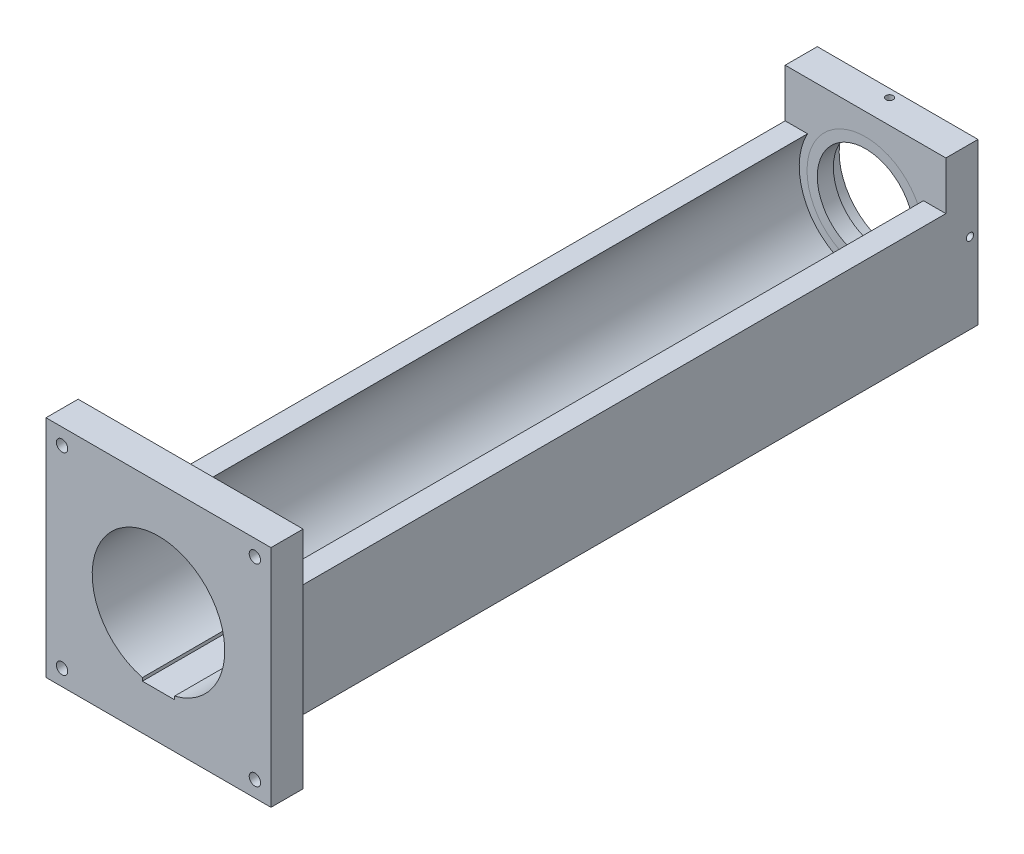
SolidWorks part; units mm, degrees
ref_plane "Front Plane" through (0, 0, 0) normal (0, 0, 1) x (1, 0, 0)
ref_plane "Top Plane" through (0, 0, 0) normal (0, 1, 0) x (1, 0, 0)
ref_plane "Right Plane" through (0, 0, 0) normal (1, 0, 0) x (0, 0, -1)
sketch "Sketch2" plane through (0, 0, 0) normal (0, 0, 1) x (1, 0, 0)
  line L1 (0, 0) -> (63.5, 0)
  line L2 (0, 0) -> (0, 63.5)
  line L3 (0, 63.5) -> (63.5, 63.5)
  line L4 (63.5, 0) -> (63.5, 63.5)
  circle A0 centre (31.75, 31.75) radius 26.1938
  dimension "D3" = 52.3875
  dimension "D4" = 31.75
  dimension "D5" = 31.75
  dimension "D6" = 31.75
  dimension "D7" = 31.75
  dimension "D1" = 63.5
  dimension "D2" = 63.5
extrude "Boss-Extrude1" add sketch "Sketch2" along normal blind 279.4
sketch "Sketch3" plane through (0, 0, 279.4) normal (0, 0, 1) x (1, 0, 0)
  line L0 (63.5, 0) -> (63.5, 63.5) construction
  line L1 (63.5, 63.5) -> (0, 63.5) construction
  line L2 (-12.7, 76.2) -> (76.2, 76.2)
  line L3 (-12.7, 76.2) -> (-12.7, -12.7)
  line L4 (-12.7, -12.7) -> (76.2, -12.7)
  line L5 (76.2, 76.2) -> (76.2, -12.7)
  line L6 (0, 0) -> (63.5, 0) construction
  line L8 (0, -34.925) -> (0, 34.925) construction
  circle A0 centre (31.75, 31.75) radius 26.1938
  circle A4 centre (31.75, 31.75) radius 26.1938 construction
  dimension "D5" = 0
  dimension "D6" = 0
  dimension "D1" = 12.7
  dimension "D2" = 12.7
  dimension "D3" = 12.7
  dimension "D4" = 12.7
extrude "Boss-Extrude2" add sketch "Sketch3" against normal blind 12.7
sketch "Sketch4" plane through (0, 0, 0) normal (0, 0, -1) x (-1, 0, 0)
  line L0 (0, 34.925) -> (0, -34.925) construction
  line L1 (-63.5, 0) -> (0, 0)
  line L2 (-63.5, 0) -> (-63.5, 63.5)
  line L3 (-63.5, 63.5) -> (0, 63.5)
  line L4 (0, 0) -> (0, 63.5)
  line L5 (-63.5, 0) -> (0, 63.5) construction
  line L6 (-63.5, 63.5) -> (0, 0) construction
  line L7 (-63.5, 63.5) -> (0, 63.5) construction
  circle A0 centre (-31.75, 31.75) radius 23.114
  circle A1 centre (-31.75, 31.75) radius 26.1938 construction
  dimension "D1" = 46.228
  dimension "D2" = 0
extrude "Boss-Extrude3" add sketch "Sketch4" along normal blind 12.7
ref_plane "Plane1" through (0, 0, -6.35) normal (0, 0, -1) x (-1, 0, 0)
sketch "Sketch5" plane through (0, 0, -6.35) normal (0, 0, -1) x (-1, 0, 0)
  circle A0 centre (-31.75, 31.75) radius 23.114
  circle A1 centre (-31.75, 31.75) radius 19.05
  circle A2 centre (-31.75, 31.75) radius 23.114 construction
  dimension "D1" = 38.1
  dimension "D2" = 0
extrude "Boss-Extrude4" add sketch "Sketch5" against normal blind 6.35 separate body
sketch "Sketch7" plane through (63.5, 0, 0) normal (1, 0, 0) x (0, 0, -1)
  line L0 (0, 48.895) -> (0, -48.895) construction
  line L1 (-266.7, 63.5) -> (0, 63.5)
  line L2 (-266.7, 63.5) -> (-266.7, 44.45)
  line L3 (-266.7, 44.45) -> (0, 44.45)
  line L4 (0, 63.5) -> (0, 44.45)
  dimension "D1" = 19.05
extrude "Cut-Extrude2" cut sketch "Sketch7" against normal through all
hole_wizard "#6-40 Tapped Hole1" positions "Sketch9" profile "Sketch8" tap size "#6-40" standard "ANSI Inch" end condition through all
sketch "Sketch9" plane through (63.5, 0, 0) normal (1, 0, 0) x (0, 0, -1)
  line L0 (12.7, 63.5) -> (12.7, 0) construction
  line L1 (0, 63.5) -> (12.7, 63.5) construction
  line L2 (48.895, 0) -> (-48.895, 0) construction
  point P0 (9.525, 31.75)
  dimension "D1" = 3.175
  dimension "D2" = 31.75
  dimension "D3" = 31.75
sketch "Sketch8" plane through (63.5, 31.75, -9.525) normal (0, 1, 0) x (0, 0, -1)
  line L0 (0, 0) -> (0, 76.2)
  line L1 (0, 76.2) -> (1.4351, 76.2)
  line L2 (1.4351, 76.2) -> (1.4351, 0)
  line L5 (1.4351, 0) -> (0, 0)
  line L11 (0, -6.35) -> (0, 107.95) construction
  dimension "Thru Tap Drill Dia." = 2.8702
  dimension "Thru Tap Drill Depth" = 76.2
cosmetic thread "Hole Thread1" parameters "D2"=3.5052
hole_wizard "#6-40 Tapped Hole2" positions "Sketch11" profile "Sketch10" tap size "#6-40" standard "ANSI Inch" end condition through all
sketch "Sketch11" plane through (0, 63.5, 0) normal (0, 1, 0) x (1, 0, 0)
  line L0 (63.5, 0) -> (63.5, 12.7) construction
  line L1 (0, 12.7) -> (63.5, 12.7) construction
  point P0 (31.75, 9.525)
  dimension "D1" = 31.75
  dimension "D2" = 3.175
sketch "Sketch10" plane through (31.75, 63.5, -9.525) normal (1, 0, 0) x (0, 0, 1)
  line L0 (0, 0) -> (0, 76.2)
  line L1 (0, 76.2) -> (1.4351, 76.2)
  line L2 (1.4351, 76.2) -> (1.4351, 0)
  line L5 (1.4351, 0) -> (0, 0)
  line L11 (0, -6.35) -> (0, 107.95) construction
  dimension "Thru Tap Drill Dia." = 2.8702
  dimension "Thru Tap Drill Depth" = 76.2
cosmetic thread "Hole Thread2" parameters "D2"=3.5052
hole_wizard "CSK for #8 Flat Head Machine Screw1" positions "Sketch14" profile "Sketch12" countersink size "#8" standard "ANSI Inch" end condition through all
sketch "Sketch14" plane through (0, 0, 266.7) normal (0, 0, -1) x (-1, 0, 0)
  line L0 (-76.2, -12.7) -> (-76.2, 76.2) construction
  line L1 (12.7, 76.2) -> (12.7, -12.7) construction
  line L3 (12.7, -12.7) -> (-76.2, -12.7) construction
  point P0 (-69.85, 69.85)
  point P2 (6.35, 69.85)
  point P4 (6.35, -6.35)
  point P6 (-69.85, -6.35)
  dimension "D1" = 76.2
  dimension "D2" = 6.35
  dimension "D3" = 6.35
  dimension "D4" = 76.2
  dimension "D5" = 6.35
  dimension "D6" = 76.2
  dimension "D7" = 76.2
  dimension "D8" = 6.35
  dimension "D9" = 6.35
sketch "Sketch12" plane through (69.85, 69.85, 266.7) normal (1, 0, 0) x (0, 1, 0)
  line L0 (0, 0) -> (0, 12.7)
  line L1 (0, 12.7) -> (2.2479, 12.7)
  line L2 (2.2479, 12.7) -> (2.2479, 2.2645)
  line L3 (2.2479, 2.2645) -> (4.2164, 0)
  line L5 (4.2164, 0) -> (0, 0)
  line L6 (-2.2479, 2.2645) -> (-4.2164, 0) construction
  line L11 (0, -6.35) -> (0, 107.95) construction
  dimension "Thru Hole Dia." = 4.4958
  dimension "Thru Hole Depth" = 12.7
  dimension "Near C'Sink Dia." = 8.4328
  dimension "Near C'Sink Angle" = 82
sketch "Sketch16" plane through (0, 0, 279.4) normal (0, 0, 1) x (1, 0, 0)
  line L0 (76.2, -12.7) -> (76.2, 76.2) construction
  line L1 (25.4, 5.08) -> (38.1, 5.08)
  line L2 (25.4, 5.08) -> (25.4, 7.6835)
  line L3 (25.4, 7.6835) -> (38.1, 7.6835)
  line L4 (38.1, 5.08) -> (38.1, 7.6835)
  line L5 (-12.7, 76.2) -> (-12.7, -12.7) construction
  arc A0 (8.841, 44.45) -> (54.659, 44.45) centre (31.75, 31.75) ccw construction
  dimension "D1" = 26.67
  dimension "D2" = 12.7
  dimension "D3" = 38.1
  dimension "D4" = 38.1
extrude "Cut-Extrude3" cut sketch "Sketch16" against normal blind 279.4
hole_wizard "1/4-20 Tapped Hole1" positions "Sketch18" profile "Sketch19" tap size "1/4-20" standard "ANSI Inch"
sketch "Sketch18" plane through (0, 0, 0) normal (0, -1, 0) x (-1, 0, 0)
  line L0 (0, 48.895) -> (0, -48.895) construction
  line L1 (-63.5, -266.7) -> (-63.5, 12.7) construction
  line L2 (0, -266.7) -> (-63.5, -266.7) construction
  line L3 (-48.895, 0) -> (48.895, 0) construction
  point P7 (-50.8, -50.8)
  point P9 (-12.7, -215.9)
  dimension "D1" = 12.7
  dimension "D2" = 12.7
  dimension "D3" = 50.8
  dimension "D4" = 50.8
sketch "Sketch19" plane through (50.8, 0, 50.8) normal (1, 0, 0) x (0, 0, -1)
  line L0 (0, 0) -> (0, 11.6938)
  line L1 (0, 11.6938) -> (2.5527, 10.16)
  line L2 (2.5527, 10.16) -> (2.5527, 0)
  line L5 (2.5527, 0) -> (0, 0)
  line L10 (0, 11.6938) -> (-2.5527, 10.16) construction
  line L11 (0, -6.35) -> (0, 107.95) construction
  dimension "Tap Drill Dia." = 5.1054
  dimension "Tap Drill Depth" = 10.16
  dimension "Drill Angle" = 118
cosmetic thread "Hole Thread3" parameters "D1"=10.16, "D2"=6.35
cosmetic thread "Hole Thread4" parameters "D1"=10.16, "D2"=6.35
